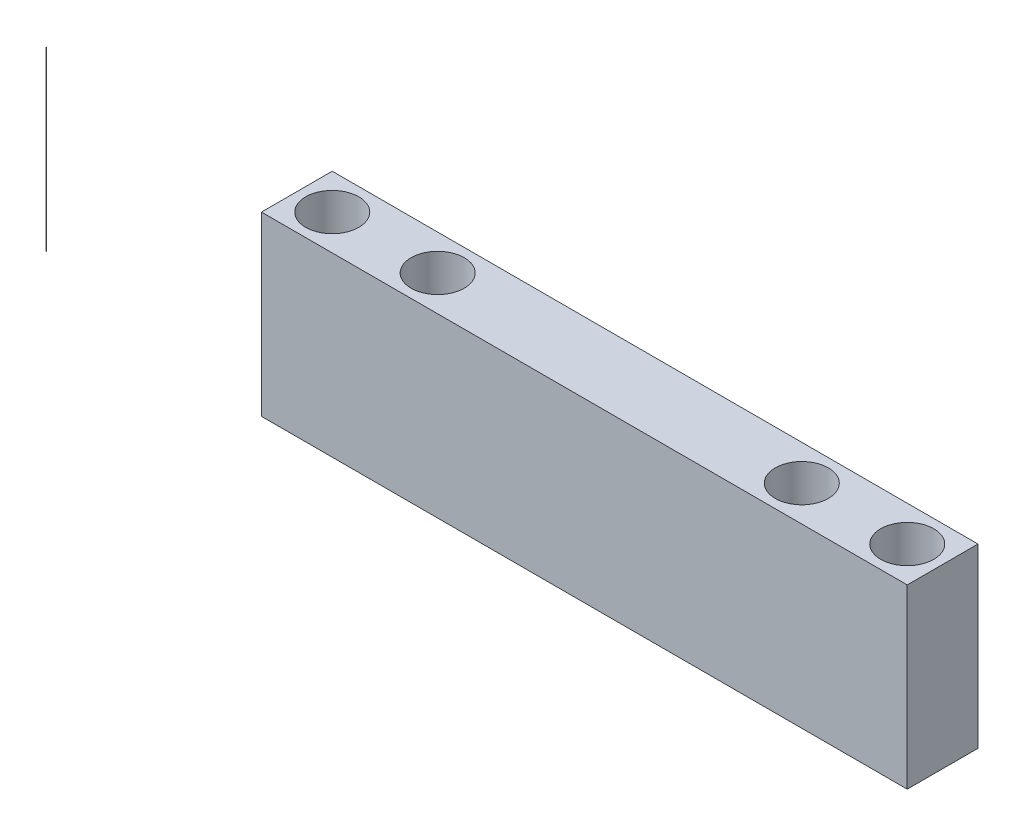
SolidWorks part; units mm, degrees
ref_plane "Front" through (0, 0, 0) normal (0, 0, 1) x (1, 0, 0)
ref_plane "Top" through (0, 0, 0) normal (0, 1, 0) x (1, 0, 0)
ref_plane "Right" through (0, 0, 0) normal (1, 0, 0) x (0, 0, -1)
sketch "Sketch1" plane through (0, 0, 0) normal (0, 1, 0) x (1, 0, 0)
  line L0 (231.775, 0) -> (-231.775, 0) construction
  line L1 (-231.775, -25.4) -> (231.775, -25.4)
  line L2 (-231.775, -25.4) -> (-231.775, 25.4)
  line L3 (-231.775, 25.4) -> (231.775, 25.4)
  line L4 (231.775, -25.4) -> (231.775, 25.4)
  line L5 (-231.775, -25.4) -> (231.775, 25.4) construction
  line L6 (-231.775, 25.4) -> (231.775, -25.4) construction
  circle A0 centre (-411.662, 0) radius 0.129
  circle A2 centre (206.375, 0) radius 19.05
  circle A3 centre (-206.375, 0) radius 19.05
  circle A4 centre (130.683, 0) radius 19.05
  circle A5 centre (-130.683, 0) radius 19.05
  point P0 (0, 0)
  point P14 (-225.425, 0)
  point P16 (225.425, 0)
  dimension "D5" = 38.1
  dimension "D1" = 50.8
  dimension "D2" = 412.75
  dimension "D3" = 6.35
  dimension "D4" = 6.35
  dimension "D6" = 75.692
  dimension "D7" = 75.692
extrude "Boss-Extrude1" add sketch "Sketch1" along normal blind 127
equation "\"D7@Sketch1\"=\"D6@Sketch1\""
